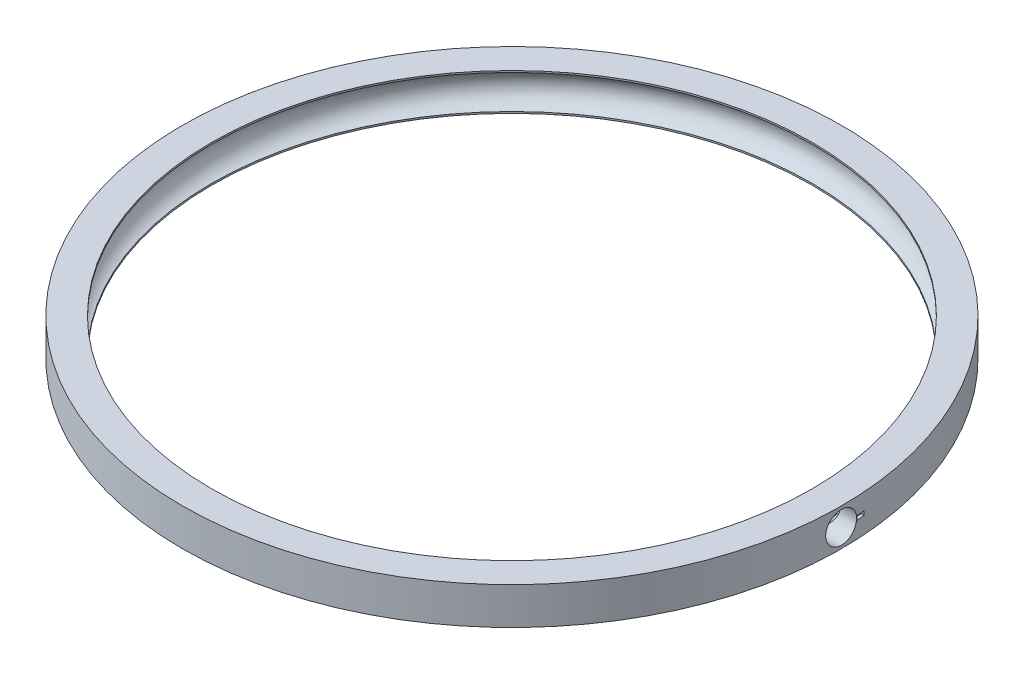
SolidWorks part; units mm, degrees
ref_plane "Front Plane" through (0, 0, 0) normal (0, 0, 1) x (1, 0, 0)
ref_plane "Top Plane" through (0, 0, 0) normal (0, 1, 0) x (1, 0, 0)
ref_plane "Right Plane" through (0, 0, 0) normal (1, 0, 0) x (0, 0, -1)
sketch "Sketch1" plane through (0, 0, 0) normal (0, 1, 0) x (1, 0, 0)
  circle A0 centre (0, 0) radius 53.25
  circle A1 centre (0, 0) radius 48.5
  dimension "D1" = 106.5
  dimension "D2" = 97
extrude "Boss-Extrude1" add sketch "Sketch1" along normal blind 6 contours A0 | A1
sketch "Sketch3" plane through (0, 0, 0) normal (0, 0, 1) x (1, 0, 0)
  line L1 (53.25, 6) -> (-53.25, 6) construction
  line L2 (0, 0) -> (0, 12.4992) construction
  line L4 (-48.5, 6) -> (-48.5, 17.212) construction
  circle A1 centre (-47.7, 3) radius 2.85
  dimension "D2" = 3
  dimension "D1" = 5.7
  dimension "D3" = 0.8
revolve "Cut-Revolve1" cut sketch "Sketch3" angle 360 about L2
sketch "Sketch4" plane through (0, 0, 0) normal (1, 0, 0) x (0, 0, -1)
  line L0 (-53.25, 0) -> (53.25, 0) construction
  circle A0 centre (0, 3) radius 2.5
  dimension "D1" = 5
  dimension "D2" = 3
extrude "Cut-Extrude1" cut sketch "Sketch4" along normal blind 120
sketch "Sketch6" plane through (0, 0, 0) normal (1, 0, 0) x (0, 0, -1)
  line L1 (2.5566, 3.3258) -> (3.7969, 3.3258)
  line L2 (2.5566, 3.3258) -> (2.5566, 2.6742)
  line L3 (2.5566, 2.6742) -> (3.7969, 2.6742)
  line L4 (3.7969, 3.3258) -> (3.7969, 2.6742)
  line L5 (2.5566, 3.3258) -> (3.7969, 2.6742) construction
  line L6 (2.5566, 2.6742) -> (3.7969, 3.3258) construction
  point P0 (3.1767, 3)
extrude "Cut-Extrude2" cut sketch "Sketch6" against normal blind 0.5 from surface starting at face at (0, 6, 53.25)
equation "\"inner_diameter\"= 90mm"
equation "\"D2@Sketch1\"=\"inner_diameter\"+7"
equation "\"D1@Sketch1\"=\"inner_diameter\"+16.5"
